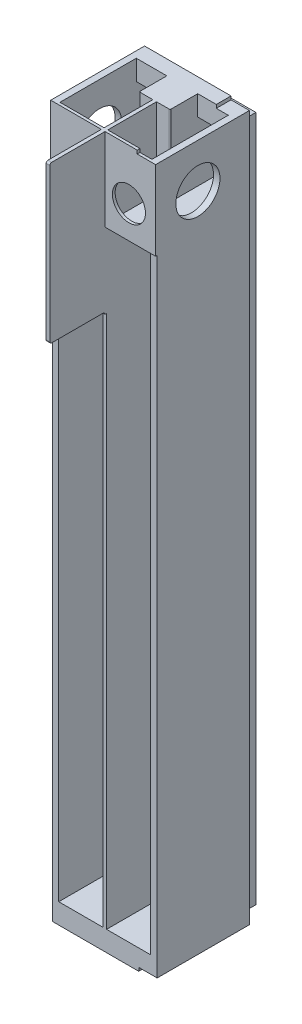
SolidWorks part; units mm, degrees
material "ABS"
ref_plane "Płaszczyzna przednia" through (0, 0, 0) normal (0, 0, 1) x (1, 0, 0)
ref_plane "Płaszczyzna górna" through (0, 0, 0) normal (0, 1, 0) x (1, 0, 0)
ref_plane "Płaszczyzna prawa" through (0, 0, 0) normal (1, 0, 0) x (0, 0, -1)
sketch "Szkic1" plane through (0, 0, 0) normal (0, 0, 1) x (1, 0, 0)
  line L0 (-90.4269, 49.2609) -> (-90.4269, -315.7391)
  line L1 (-91.9269, 53.7609) -> (-38.9269, 53.7609)
  line L2 (-91.9269, 53.7609) -> (-91.9269, -320.2391)
  line L3 (-91.9269, -320.2391) -> (-38.9269, -320.2391)
  line L4 (-38.9269, 53.7609) -> (-38.9269, -320.2391)
  line L5 (-40.4269, 49.2609) -> (-64.4269, 49.2609)
  line L6 (-90.4269, -315.7391) -> (-66.4269, -315.7391)
  line L7 (-90.4269, 49.2609) -> (-66.4269, 49.2609)
  line L8 (-66.4269, 49.2609) -> (-66.4269, -315.7391)
  line L10 (-64.4269, 49.2609) -> (-64.4269, -315.7391)
  line L13 (-40.4269, 49.2609) -> (-40.4269, -315.7391)
  line L14 (-40.4269, -315.7391) -> (-64.4269, -315.7391)
  dimension "D1" = 374
  dimension "D2" = 24
  dimension "D3" = 53
  dimension "D4" = 365
extrude "Dodanie-wyciągnięcie2" add sketch "Szkic1" along normal blind 12 contours L3 L4 L1 L2 | L6 L8 L7 L0 | L14 L10 L5 L13
sketch "Szkic2" plane through (-66.4269, 0, 0) normal (-1, 0, 0) x (0, 0, 1)
  line L0 (12, 49.2609) -> (12, -315.7391) construction
  line L1 (0, 49.2609) -> (12, 49.2609)
  line L2 (0, 49.2609) -> (0, 45.7609)
  line L3 (0, 45.7609) -> (12, 45.7609)
  line L4 (12, 49.2609) -> (12, 45.7609)
extrude "Wytnij-wyciągnięcie1" cut sketch "Szkic2" against normal blind 2
ref_plane "Płaszczyzna1" through (0, 0, 12) normal (0, 0, 1) x (1, 0, 0)
sketch "Szkic3" plane through (0, 0, 12) normal (0, 0, 1) x (1, 0, 0)
  line L6 (-38.9269, -320.2391) -> (-91.9269, -320.2391)
  line L7 (-38.9269, -320.2391) -> (-38.9269, 53.7609)
  line L8 (-38.9269, 53.7609) -> (-91.9269, 53.7609)
  line L9 (-91.9269, -320.2391) -> (-91.9269, 53.7609)
extrude "Dodanie-wyciągnięcie3" add sketch "Szkic3" along normal blind 2
sketch "Szkic4" plane through (0, 0, 14) normal (0, 0, 1) x (1, 0, 0)
  line L64 (-46.9269, -11.0391) -> (-56.3269, -11.0391)
  line L69 (-90.4269, 49.2609) -> (-40.4269, 49.2609) construction
  line L70 (-53.7269, 49.2609) -> (-40.4269, 49.2609)
  line L71 (-40.4269, 49.2609) -> (-40.4269, 18.7608)
  line L72 (-40.4269, 49.2609) -> (-40.4269, -315.7391) construction
  line L73 (-40.4269, 18.7608) -> (-53.7269, 18.7608)
  line L74 (-53.7269, 49.2609) -> (-53.7269, 18.7608)
  line L77 (-77.1269, 49.2609) -> (-77.1269, 18.7608)
  line L78 (-90.4269, 18.7608) -> (-77.1269, 18.7608)
  line L79 (-90.4269, 49.2609) -> (-90.4269, 18.7608)
  line L80 (-77.1269, 49.2609) -> (-90.4269, 49.2609)
  line L81 (-46.9269, -35.3991) -> (-46.9269, -40.4791)
  line L82 (-46.9269, -40.4791) -> (-56.3269, -40.4791)
  line L87 (-46.9269, -35.3991) -> (-46.9269, -11.0391)
  line L89 (-56.3269, -35.3991) -> (-56.3269, -11.0391)
  line L90 (-74.5269, -35.3991) -> (-74.5269, -11.0391)
  line L92 (-83.9269, -35.3991) -> (-83.9269, -11.0391)
  line L93 (-83.9269, -11.0391) -> (-74.5269, -11.0391)
  line L94 (-46.9269, -101.2391) -> (-46.9269, -166.1991)
  line L95 (-46.9269, -166.1991) -> (-56.3269, -166.1991)
  line L96 (-46.9269, -101.2391) -> (-56.3269, -101.2391)
  line L97 (-56.3269, -166.1991) -> (-56.3269, -101.2391)
  line L98 (-74.5269, -166.1991) -> (-74.5269, -101.2391)
  line L99 (-83.9269, -101.2391) -> (-74.5269, -101.2391)
  line L100 (-83.9269, -166.1991) -> (-74.5269, -166.1991)
  line L101 (-83.9269, -101.2391) -> (-83.9269, -166.1991)
  line L102 (-56.3269, -40.4791) -> (-56.3269, -35.3991)
  line L103 (-74.5269, -35.3991) -> (-74.5269, -40.4791)
  line L104 (-74.5269, -40.4791) -> (-83.9269, -40.4791)
  line L105 (-83.9269, -40.4791) -> (-83.9269, -35.3991)
extrude "Wytnij-wyciągnięcie2" cut sketch "Szkic4" against normal blind 2
sketch "Szkic5" plane through (0, 0, 14) normal (0, 0, 1) x (1, 0, 0)
  line L1 (-91.9269, -320.2391) -> (-38.9269, -320.2391) construction
  line L7 (-64.4269, -320.2391) -> (-66.4269, -320.2391)
  line L11 (-64.4269, -320.2391) -> (-64.4269, 53.7609)
  line L12 (-64.4269, 53.7609) -> (-66.4269, 53.7609)
  line L13 (-66.4269, -320.2391) -> (-66.4269, 53.7609)
extrude "Dodanie-wyciągnięcie4" add sketch "Szkic5" along normal blind 43
sketch "Szkic6" plane through (0, 0, 14) normal (0, 0, 1) x (1, 0, 0)
  line L0 (-64.4269, 16.7608) -> (-40.4269, 16.7608)
  line L4 (-64.4269, -320.2391) -> (-64.4269, 53.7609) construction
  line L5 (-40.4269, 49.2609) -> (-40.4269, -315.7391) construction
  line L6 (-40.4269, 16.7608) -> (-40.4269, 53.7609)
  line L7 (-91.9269, 53.7609) -> (-38.9269, 53.7609) construction
  line L8 (-40.4269, 53.7609) -> (-38.9269, 53.7609)
  line L19 (-90.4269, 53.7609) -> (-91.9269, 53.7609)
  line L20 (-90.4269, 16.7608) -> (-90.4269, 53.7609)
  line L21 (-66.4269, 16.7608) -> (-90.4269, 16.7608)
  line L22 (-64.4269, 16.7608) -> (-64.4269, 15.2608)
  line L23 (-64.4269, 15.2608) -> (-38.9269, 15.2608)
  line L24 (-38.9269, 15.2608) -> (-38.9269, 53.7609)
  line L25 (-91.9269, 15.2608) -> (-91.9269, 53.7609)
  line L26 (-66.4269, 15.2608) -> (-91.9269, 15.2608)
  line L27 (-66.4269, 16.7608) -> (-66.4269, 15.2608)
extrude "Dodanie-wyciągnięcie5" add sketch "Szkic6" along normal blind 41.5
ref_plane "Płaszczyzna2" through (0, 0, 55.5) normal (0, 0, 1) x (1, 0, 0)
sketch "Szkic7" plane through (0, 0, 55.5) normal (0, 0, 1) x (1, 0, 0)
  line L1 (-38.9269, 15.2608) -> (-64.4269, 15.2608)
  line L2 (-38.9269, 15.2608) -> (-38.9269, 53.7609)
  line L3 (-38.9269, 53.7609) -> (-64.4269, 53.7609)
  line L4 (-64.4269, 15.2608) -> (-64.4269, 53.7609)
  line L5 (-66.4269, 15.2608) -> (-91.9269, 15.2608)
  line L6 (-66.4269, 15.2608) -> (-66.4269, 53.7609)
  line L7 (-66.4269, 53.7609) -> (-91.9269, 53.7609)
  line L8 (-91.9269, 15.2608) -> (-91.9269, 53.7609)
extrude "Dodanie-wyciągnięcie6" add sketch "Szkic7" along normal blind 1.5
sketch "Szkic9" plane through (-91.9269, 0, 0) normal (-1, 0, 0) x (0, 0, 1)
  circle A1 centre (34, 34.5109) radius 12
extrude "Wytnij-wyciągnięcie4" cut sketch "Szkic9" against normal blind 1.5
sketch "Szkic10" plane through (0, 0, 14) normal (0, 0, 1) x (1, 0, 0)
  line L0 (-91.9269, 15.2608) -> (-91.9269, -320.2391)
  line L1 (-91.9269, -320.2391) -> (-66.4269, -320.2391)
  line L2 (-66.4269, -320.2391) -> (-66.4269, -315.7391)
  line L3 (-66.4269, 15.2608) -> (-66.4269, -320.2391) construction
  line L4 (-66.4269, -315.7391) -> (-90.4269, -315.7391)
  line L5 (-90.4269, -315.7391) -> (-90.4269, 15.2608)
  line L6 (-91.9269, 15.2608) -> (-66.4269, 15.2608) construction
  line L7 (-90.4269, 15.2608) -> (-91.9269, 15.2608)
  dimension "D1" = 330.9999
  dimension "D2" = 24
extrude "Dodanie-wyciągnięcie7" add sketch "Szkic10" along normal blind 43
sketch "Szkic11" plane through (0, 0, 14) normal (0, 0, 1) x (1, 0, 0)
  line L0 (-38.9269, 15.2608) -> (-38.9269, -320.2391)
  line L1 (-38.9269, -320.2391) -> (-64.4269, -320.2391)
  line L2 (-64.4269, -320.2391) -> (-64.4269, -315.7391)
  line L3 (-64.4269, -320.2391) -> (-64.4269, 15.2608) construction
  line L4 (-64.4269, -315.7391) -> (-40.4269, -315.7391)
  line L5 (-40.4269, -315.7391) -> (-40.4269, 15.2608)
  line L6 (-64.4269, 15.2608) -> (-38.9269, 15.2608) construction
  line L7 (-40.4269, 15.2608) -> (-38.9269, 15.2608)
  dimension "D1" = 330.9999
  dimension "D2" = 24
extrude "Dodanie-wyciągnięcie8" add sketch "Szkic11" along normal blind 43
sketch "Szkic12" plane through (-38.9269, 0, 0) normal (1, 0, 0) x (0, 0, -1)
  circle A0 centre (-34, 34.5109) radius 12
extrude "Wytnij-wyciągnięcie5" cut sketch "Szkic12" against normal blind 1.5
sketch "Szkic13" plane through (0, 0, 57) normal (0, 0, 1) x (1, 0, 0)
  circle A2 centre (-51.4269, 32.8109) radius 9
  circle A3 centre (-79.4269, 32.8109) radius 9
extrude "Wytnij-wyciągnięcie6" cut sketch "Szkic13" against normal blind 1.5
sketch "Szkic14" plane through (-38.9269, 0, 0) normal (1, 0, 0) x (0, 0, -1)
  line L1 (-57, -320.2391) -> (0, -320.2391)
  line L2 (-57, -320.2391) -> (-57, 53.7609)
  line L3 (-57, 53.7609) -> (0, 53.7609)
  line L4 (0, -320.2391) -> (0, 53.7609)
  circle A0 centre (-34, 34.5109) radius 12
extrude "Dodanie-wyciągnięcie9" add sketch "Szkic14" along normal blind 1
sketch "Szkic15" plane through (-91.9269, 0, 0) normal (-1, 0, 0) x (0, 0, 1)
  line L1 (57, 53.7609) -> (0, 53.7609)
  line L2 (57, 53.7609) -> (57, -320.2391)
  line L3 (57, -320.2391) -> (0, -320.2391)
  line L4 (0, 53.7609) -> (0, -320.2391)
  circle A0 centre (34, 34.5109) radius 12
extrude "Dodanie-wyciągnięcie10" add sketch "Szkic15" along normal blind 1
sketch "Szkic16" plane through (0, 53.7609, 0) normal (0, 1, 0) x (1, 0, 0)
  line L1 (-37.9269, -57) -> (-92.9269, -57)
  line L2 (-37.9269, -57) -> (-37.9269, 0)
  line L3 (-37.9269, 0) -> (-92.9269, 0)
  line L4 (-92.9269, -57) -> (-92.9269, 0)
  line L5 (-40.4269, -55.5) -> (-64.4269, -55.5)
  line L6 (-40.4269, -55.5) -> (-40.4269, -14)
  line L7 (-40.4269, -14) -> (-64.4269, -14)
  line L8 (-64.4269, -55.5) -> (-64.4269, -14)
  line L9 (-66.4269, -55.5) -> (-90.4269, -55.5)
  line L10 (-66.4269, -55.5) -> (-66.4269, -14)
  line L11 (-66.4269, -14) -> (-90.4269, -14)
  line L12 (-90.4269, -55.5) -> (-90.4269, -14)
extrude "Dodanie-wyciągnięcie11" add sketch "Szkic16" along normal blind 1
sketch "Szkic17" plane through (0, -320.2391, 0) normal (0, -1, 0) x (1, 0, 0)
  line L1 (-92.9269, 57) -> (-37.9269, 57)
  line L2 (-92.9269, 57) -> (-92.9269, 0)
  line L3 (-92.9269, 0) -> (-37.9269, 0)
  line L4 (-37.9269, 57) -> (-37.9269, 0)
extrude "Dodanie-wyciągnięcie12" add sketch "Szkic17" along normal blind 1
sketch "Szkic18" plane through (0, 0, 57) normal (0, 0, 1) x (1, 0, 0)
  line L0 (-64.4269, 15.2608) -> (-64.4269, 54.7609)
  line L2 (-66.4269, 15.2608) -> (-66.4269, 54.7609)
  line L3 (-66.4269, 54.7609) -> (-64.4269, 54.7609)
  line L4 (-66.4269, 15.2608) -> (-66.4269, -4.7392)
  line L5 (-66.4269, 15.2608) -> (-66.4269, -315.7391) construction
  line L7 (-64.4269, -315.7391) -> (-64.4269, 15.2608) construction
  line L8 (-64.4269, -4.7392) -> (-64.4269, 15.2608)
  line L9 (-66.4269, -4.7392) -> (-66.4269, -24.7392)
  line L10 (-66.4269, 15.2608) -> (-66.4269, -315.7391) construction
  line L11 (-66.4269, -24.7392) -> (-64.4269, -24.7392)
  line L12 (-64.4269, -315.7391) -> (-64.4269, 15.2608) construction
  line L13 (-64.4269, -24.7392) -> (-64.4269, -4.7392)
extrude "Dodanie-wyciągnięcie13" add sketch "Szkic18" along normal blind 30
sketch "Szkic20" plane through (0, -321.2391, 0) normal (0, -1, 0) x (1, 0, 0)
  line L1 (-92.9269, 57) -> (-37.9269, 57)
  line L2 (-92.9269, 57) -> (-92.9269, 0)
  line L3 (-92.9269, 0) -> (-37.9269, 0)
  line L4 (-37.9269, 57) -> (-37.9269, 0)
extrude "Dodanie-wyciągnięcie14" add sketch "Szkic20" along normal blind 5.5
sketch "Szkic21" plane through (0, 54.7609, 0) normal (0, 1, 0) x (1, 0, 0)
  line L0 (-64.4269, -87) -> (-66.4269, -87)
  line L1 (-66.4269, -87) -> (-66.4269, -57)
  line L2 (-66.4269, -57) -> (-92.9269, -57)
  line L3 (-92.9269, -57) -> (-92.9269, 0)
  line L4 (-92.9269, 0) -> (-37.9269, 0)
  line L5 (-37.9269, 0) -> (-37.9269, -57)
  line L6 (-37.9269, -57) -> (-64.4269, -57)
  line L7 (-64.4269, -57) -> (-64.4269, -87)
  line L9 (-40.4269, -55.5) -> (-64.4269, -55.5)
  line L10 (-40.4269, -55.5) -> (-40.4269, -14)
  line L11 (-40.4269, -14) -> (-64.4269, -14)
  line L12 (-64.4269, -55.5) -> (-64.4269, -14)
  line L13 (-66.4269, -55.5) -> (-90.4269, -55.5)
  line L14 (-66.4269, -55.5) -> (-66.4269, -14)
  line L15 (-66.4269, -14) -> (-90.4269, -14)
  line L16 (-90.4269, -55.5) -> (-90.4269, -14)
extrude "Dodanie-wyciągnięcie15" add sketch "Szkic21" along normal blind 5.5
sketch "Szkic22" plane through (-37.9269, 0, 0) normal (1, 0, 0) x (0, 0, -1)
  line L1 (-57, -326.7391) -> (0, -326.7391)
  line L2 (-57, -326.7391) -> (-57, 60.2609)
  line L3 (-57, 60.2609) -> (0, 60.2609)
  line L4 (0, -326.7391) -> (0, 60.2609)
  circle A0 centre (-34, 34.5109) radius 12
  dimension "D1" = 24
extrude "Dodanie-wyciągnięcie16" add sketch "Szkic22" along normal blind 1
sketch "Szkic23" plane through (-92.9269, 0, 0) normal (-1, 0, 0) x (0, 0, 1)
  line L1 (57, 60.2609) -> (0, 60.2609)
  line L2 (57, 60.2609) -> (57, -326.7391)
  line L3 (57, -326.7391) -> (0, -326.7391)
  line L4 (0, 60.2609) -> (0, -326.7391)
  circle A0 centre (34, 34.5109) radius 12
extrude "Dodanie-wyciągnięcie17" add sketch "Szkic23" along normal blind 1
fillet "Zaokrąglenie1" radius 1 1 edges at (-65.4269, -24.7392, 87)
fillet "Zaokrąglenie2" radius 1 1 edges at (-65.4269, -24.7392, 57)
fillet "Zaokrąglenie3" radius 1 1 edges at (-65.4269, 60.2609, 87)
sketch "Szkic24" plane through (0, 0, 0) normal (0, 0, -1) x (-1, 0, 0)
  line L14 (91.4269, -319.7391) -> (39.4269, -319.7391)
  line L15 (91.4269, -319.7391) -> (91.4269, 53.2609)
  line L16 (91.4269, 53.2609) -> (39.4269, 53.2609)
  line L17 (39.4269, -319.7391) -> (39.4269, 53.2609)
  line L18 (36.9269, 60.2609) -> (93.9269, 60.2609)
  line L19 (36.9269, 60.2609) -> (36.9269, -326.7391)
  line L20 (36.9269, -326.7391) -> (93.9269, -326.7391)
  line L21 (93.9269, 60.2609) -> (93.9269, -326.7391)
extrude "Wytnij-wyciągnięcie7" cut sketch "Szkic24" against normal blind 6
sketch "Szkic25" plane through (0, 0, 14) normal (0, 0, 1) x (1, 0, 0)
  line L1 (-64.4269, -315.7391) -> (-40.4269, -315.7391)
  line L2 (-64.4269, -315.7391) -> (-64.4269, 15.2608)
  line L3 (-64.4269, 15.2608) -> (-40.4269, 15.2608)
  line L4 (-40.4269, -315.7391) -> (-40.4269, 15.2608)
  line L5 (-90.4269, -315.7391) -> (-66.4269, -315.7391)
  line L6 (-90.4269, -315.7391) -> (-90.4269, 15.2608)
  line L7 (-90.4269, 15.2608) -> (-66.4269, 15.2608)
  line L8 (-66.4269, -315.7391) -> (-66.4269, 15.2608)
extrude "Wytnij-wyciągnięcie8" cut sketch "Szkic25" against normal blind 2
sketch "Szkic26" plane through (0, 60.2609, 0) normal (0, 1, 0) x (1, 0, 0)
  line L0 (-36.9269, -57) -> (-46.9269, -57)
  line L1 (-64.4269, -57) -> (-36.9269, -57) construction
  line L2 (-46.9269, -57) -> (-46.9269, -6)
  line L3 (-93.9269, -6) -> (-36.9269, -6) construction
  line L4 (-46.9269, -6) -> (-36.9269, -6)
  line L5 (-36.9269, -6) -> (-36.9269, -57)
extrude "Wytnij-wyciągnięcie9" cut sketch "Szkic26" against normal blind 1.85
sketch "Szkic27" plane through (0, -326.7391, 0) normal (0, -1, 0) x (1, 0, 0)
  line L0 (-36.9269, 57) -> (-46.9269, 57)
  line L1 (-36.9269, 57) -> (-93.9269, 57) construction
  line L2 (-46.9269, 57) -> (-46.9269, 6)
  line L3 (-36.9269, 6) -> (-93.9269, 6) construction
  line L4 (-46.9269, 6) -> (-36.9269, 6)
  line L5 (-36.9269, 6) -> (-36.9269, 57)
extrude "Wytnij-wyciągnięcie10" cut sketch "Szkic27" against normal blind 1.85
sketch "Szkic28" plane through (0, 0, 57) normal (0, 0, 1) x (1, 0, 0)
  line L0 (-36.9269, -324.8891) -> (-46.9269, -324.8891)
  line L1 (-46.9269, -324.8891) -> (-46.9269, -326.7391)
  line L2 (-46.9269, -326.7391) -> (-93.9269, -326.7391)
  line L6 (-66.4269, -25.7392) -> (-64.4269, -25.7392)
  line L12 (-64.4269, -25.7392) -> (-64.4269, 15.2608)
  line L13 (-64.4269, 15.2608) -> (-36.9269, 15.2608)
  line L14 (-36.9269, 58.4109) -> (-36.9269, -324.8891) construction
  line L15 (-36.9269, 15.2608) -> (-36.9269, -324.8891)
  line L16 (-66.4269, -25.7392) -> (-66.4269, 15.2608)
  line L17 (-66.4269, 15.2608) -> (-93.9269, 15.2608)
  line L18 (-93.9269, -326.7391) -> (-93.9269, 60.2609) construction
  line L19 (-93.9269, 15.2608) -> (-93.9269, -326.7391)
extrude "Wytnij-wyciągnięcie11" cut sketch "Szkic28" against normal blind 0.85
sketch "Szkic29" plane through (0, 0, 14) normal (0, 0, 1) x (1, 0, 0)
  line L0 (-40.4269, 18.7608) -> (-40.4269, 16.7608)
  line L1 (-40.4269, 16.7608) -> (-64.4269, 16.7608)
  line L2 (-40.4269, 18.7608) -> (-53.7269, 18.7608)
  line L3 (-53.7269, 18.7608) -> (-53.7269, 49.2609)
  line L4 (-53.7269, 49.2609) -> (-64.4269, 49.2609)
  line L5 (-64.4269, 16.7608) -> (-64.4269, 60.2609) construction
  line L6 (-64.4269, 49.2609) -> (-64.4269, 16.7608)
extrude "Wytnij-wyciągnięcie12" cut sketch "Szkic29" against normal blind 2
sketch "Szkic30" plane through (0, 0, 14) normal (0, 0, 1) x (1, 0, 0)
  line L0 (-77.1269, 49.2609) -> (-66.4269, 49.2609)
  line L1 (-66.4269, 60.2609) -> (-66.4269, 16.7608) construction
  line L2 (-66.4269, 49.2609) -> (-66.4269, 16.7608)
  line L3 (-66.4269, 16.7608) -> (-90.4269, 16.7608)
  line L4 (-90.4269, 16.7608) -> (-90.4269, 18.7608)
  line L5 (-90.4269, 18.7608) -> (-77.1269, 18.7608)
  line L6 (-77.1269, 18.7608) -> (-77.1269, 49.2609)
extrude "Wytnij-wyciągnięcie13" cut sketch "Szkic30" against normal blind 2
sketch "Szkic31" plane through (0, 0, 12) normal (0, 0, -1) x (-1, 0, 0)
  line L1 (66.4269, 49.2609) -> (64.4269, 49.2609)
  line L2 (66.4269, 49.2609) -> (66.4269, 45.7609)
  line L3 (66.4269, 45.7609) -> (64.4269, 45.7609)
  line L4 (64.4269, 49.2609) -> (64.4269, 45.7609)
extrude "Wytnij-wyciągnięcie14" cut sketch "Szkic31" against normal blind 16
sketch "Szkic32" plane through (-64.4269, 0, 0) normal (1, 0, 0) x (0, 0, -1)
  line L0 (-28, 45.7609) -> (-28, 16.7608)
  line L1 (-55.5, 16.7608) -> (-12, 16.7608) construction
  line L2 (-28, 16.7608) -> (-30, 16.7608)
  line L3 (-30, 16.7608) -> (-30, 60.2609)
  line L4 (-14, 60.2609) -> (-55.5, 60.2609) construction
  line L5 (-30, 60.2609) -> (-28, 60.2609)
  line L6 (-28, 60.2609) -> (-28, 45.7609)
extrude "Dodanie-wyciągnięcie18" add sketch "Szkic32" along normal blind 7.4
sketch "Szkic33" plane through (-66.4269, 0, 0) normal (-1, 0, 0) x (0, 0, 1)
  line L0 (28, 49.2609) -> (28, 60.2609)
  line L1 (55.5, 60.2609) -> (14, 60.2609) construction
  line L2 (28, 60.2609) -> (30, 60.2609)
  line L3 (30, 60.2609) -> (30, 16.7608)
  line L4 (55.5, 16.7608) -> (12, 16.7608) construction
  line L5 (30, 16.7608) -> (28, 16.7608)
  line L6 (28, 16.7608) -> (28, 49.2609)
extrude "Dodanie-wyciągnięcie19" add sketch "Szkic33" along normal blind 7.4
sketch "Szkic34" plane through (0, 0, 14) normal (0, 0, 1) x (1, 0, 0)
  line L0 (-64.4269, 60.2609) -> (-57.0269, 60.2609)
  line L1 (-46.9269, 60.2609) -> (-64.4269, 60.2609) construction
  line L2 (-57.0269, 60.2609) -> (-57.0269, 49.2609)
  line L3 (-40.4269, 49.2609) -> (-64.4269, 49.2609) construction
  line L4 (-57.0269, 49.2609) -> (-64.4269, 49.2609)
  line L5 (-64.4269, 49.2609) -> (-64.4269, 60.2609) construction
  line L6 (-64.4269, 49.2609) -> (-64.4269, 60.2609)
extrude "Dodanie-wyciągnięcie20" add sketch "Szkic34" along normal blind 14
sketch "Szkic35" plane through (0, 0, 14) normal (0, 0, 1) x (1, 0, 0)
  line L0 (-66.4269, 60.2609) -> (-73.8269, 60.2609)
  line L1 (-66.4269, 60.2609) -> (-90.4269, 60.2609) construction
  line L2 (-73.8269, 60.2609) -> (-73.8269, 49.2609)
  line L3 (-66.4269, 49.2609) -> (-90.4269, 49.2609) construction
  line L4 (-73.8269, 49.2609) -> (-66.4269, 49.2609)
  line L5 (-66.4269, 49.2609) -> (-66.4269, 60.2609)
extrude "Dodanie-wyciągnięcie21" add sketch "Szkic35" along normal blind 14
sketch "Szkic36" plane through (0, 0, 28) normal (0, 0, -1) x (-1, 0, 0)
  line L0 (57.0269, 49.2609) -> (57.0269, 15.2608)
  line L1 (40.4269, 15.2608) -> (64.4269, 15.2608) construction
  line L2 (57.0269, 15.2608) -> (59.0269, 15.2608)
  line L3 (59.0269, 15.2608) -> (59.0269, 49.2609)
  line L4 (73.8269, 49.2609) -> (57.0269, 49.2609) construction
  line L5 (59.0269, 49.2609) -> (57.0269, 49.2609)
  line L6 (73.8269, 49.2609) -> (71.8269, 49.2609)
  line L7 (90.4269, 49.2609) -> (40.4269, 49.2609) construction
  line L8 (71.8269, 49.2609) -> (71.8269, 15.2608)
  line L9 (66.4269, 15.2608) -> (90.4269, 15.2608) construction
  line L10 (71.8269, 15.2608) -> (73.8269, 15.2608)
  line L11 (73.8269, 15.2608) -> (73.8269, 49.2609)
extrude "Dodanie-wyciągnięcie22" add sketch "Szkic36" along normal blind 24
sketch "Szkic37" plane through (0, 0, 12) normal (0, 0, -1) x (-1, 0, 0)
  line L1 (40.4269, 16.7608) -> (57.0269, 16.7608)
  line L2 (40.4269, 16.7608) -> (40.4269, 15.2608)
  line L3 (40.4269, 15.2608) -> (57.0269, 15.2608)
  line L4 (57.0269, 16.7608) -> (57.0269, 15.2608)
  line L5 (59.0269, 16.7608) -> (64.4269, 16.7608)
  line L6 (59.0269, 16.7608) -> (59.0269, 15.2608)
  line L7 (59.0269, 15.2608) -> (64.4269, 15.2608)
  line L8 (64.4269, 16.7608) -> (64.4269, 15.2608)
  line L9 (66.4269, 16.7608) -> (71.8269, 16.7608)
  line L10 (66.4269, 16.7608) -> (66.4269, 15.2608)
  line L11 (66.4269, 15.2608) -> (71.8269, 15.2608)
  line L12 (71.8269, 16.7608) -> (71.8269, 15.2608)
  line L13 (73.8269, 16.7608) -> (90.4269, 16.7608)
  line L14 (73.8269, 16.7608) -> (73.8269, 15.2608)
  line L15 (73.8269, 15.2608) -> (90.4269, 15.2608)
  line L16 (90.4269, 16.7608) -> (90.4269, 15.2608)
extrude "Dodanie-wyciągnięcie23" add sketch "Szkic37" along normal blind 8
sketch "Szkic38" plane through (0, 0, 30) normal (0, 0, 1) x (1, 0, 0)
  line L1 (-66.4269, 16.7608) -> (-73.8269, 16.7608)
  line L2 (-66.4269, 16.7608) -> (-66.4269, 60.2609)
  line L3 (-66.4269, 60.2609) -> (-73.8269, 60.2609)
  line L4 (-73.8269, 16.7608) -> (-73.8269, 60.2609)
  line L9 (-57.0269, 60.2609) -> (-64.4269, 60.2609)
  line L10 (-57.0269, 60.2609) -> (-57.0269, 16.7608)
  line L11 (-57.0269, 16.7608) -> (-64.4269, 16.7608)
  line L12 (-64.4269, 60.2609) -> (-64.4269, 16.7608)
extrude "Wytnij-wyciągnięcie15" cut sketch "Szkic38" against normal blind 1
fillet "Zaokrąglenie4" radius 0.5 1 edges at (-57.0269, 38.5109, 29)
fillet "Zaokrąglenie5" radius 0.5 1 edges at (-73.8269, 38.5109, 29)
